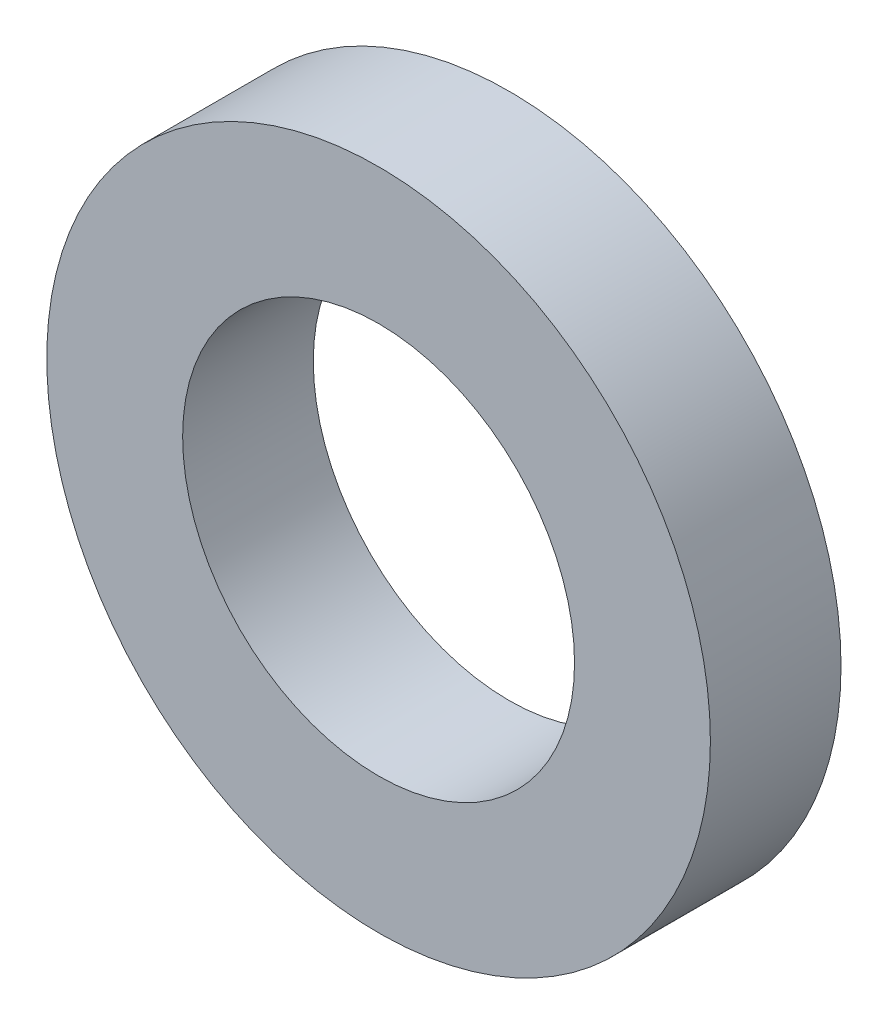
SolidWorks part; units mm, degrees
material "ABS"
ref_plane "Front Plane" through (0, 0, 0) normal (0, 0, 1) x (1, 0, 0)
ref_plane "Top Plane" through (0, 0, 0) normal (0, 1, 0) x (1, 0, 0)
ref_plane "Right Plane" through (0, 0, 0) normal (1, 0, 0) x (0, 0, -1)
sketch "Sketch1" plane through (0, 0, 0) normal (0, 0, 1) x (1, 0, 0)
  circle A0 centre (0, 0) radius 1.5
  circle A1 centre (0, 0) radius 2.54
  dimension "D1" = 3
  dimension "D2" = 5.08
extrude "Boss-Extrude1" add sketch "Sketch1" along normal mid plane 1
